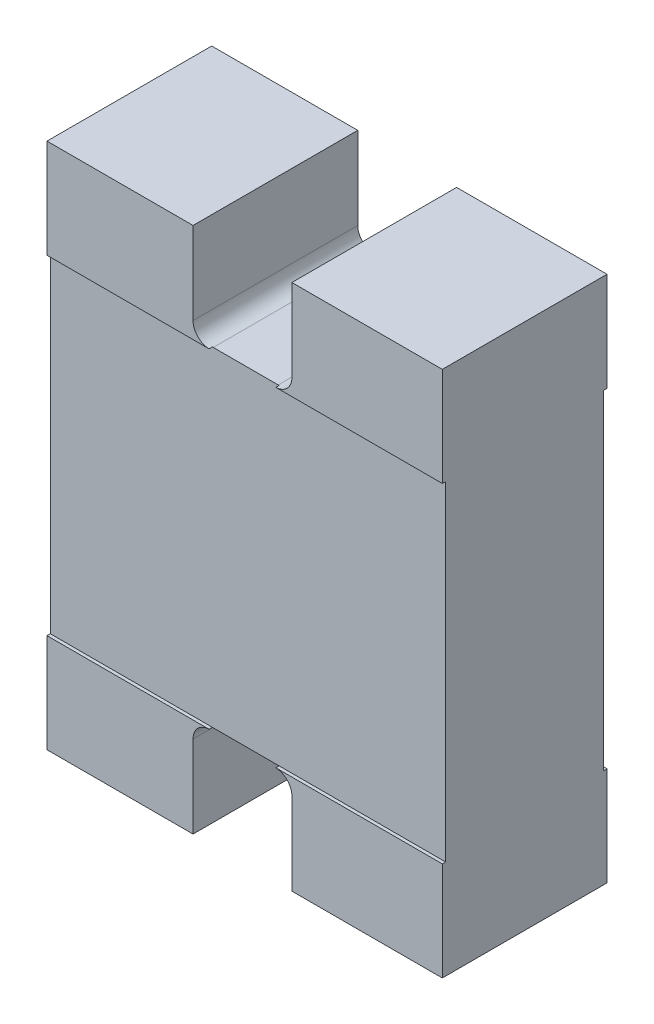
SolidWorks part; units mm, degrees
ref_plane "Front Plane" through (0, 0, 0) normal (0, 0, 1) x (1, 0, 0)
ref_plane "Top Plane" through (0, 0, 0) normal (0, 1, 0) x (1, 0, 0)
ref_plane "Right Plane" through (0, 0, 0) normal (1, 0, 0) x (0, 0, -1)
sketch "Sketch1" plane through (0, 0, 0) normal (0, 0, 1) x (1, 0, 0)
  line L1 (-0.6, 0.8) -> (0.6, 0.8)
  line L2 (-0.6, 0.8) -> (-0.6, -0.8)
  line L3 (-0.6, -0.8) -> (0.6, -0.8)
  line L4 (0.6, 0.8) -> (0.6, -0.8)
  line L5 (-0.6, 0.8) -> (0.6, -0.8) construction
  line L6 (-0.6, -0.8) -> (0.6, 0.8) construction
  point P0 (0, 0)
  dimension "D1" = 1.2
  dimension "D2" = 1.6
extrude "Boss-Extrude1" add sketch "Sketch1" along normal blind 0.5
sketch "Sketch2" plane through (0, 0, 0) normal (0, 0, -1) x (-1, 0, 0)
  line L0 (0, 0.8) -> (0, -0.8) construction
  line L1 (-0.6, 0.8) -> (0.6, 0.8) construction
  line L2 (0.6, -0.8) -> (-0.6, -0.8) construction
  line L3 (-0.6, 0) -> (0.6, 0) construction
  line L4 (-0.6, -0.8) -> (-0.6, 0.8) construction
  line L5 (0.6, 0.8) -> (0.6, -0.8) construction
  line L6 (-0.4, 0.8) -> (-0.4, -0.8) construction
  line L7 (-0.6, 0.5) -> (0.6, 0.5) construction
  line L8 (-0.1434, 0.55) -> (0.1566, 0.55) construction
  line L9 (0.1566, 0.8) -> (0.1566, 0.55)
  line L13 (-0.1434, 0.8) -> (-0.1434, 0.55)
  line L17 (-0.092, 0.5) -> (0.1052, 0.5)
  line L19 (-0.1434, 0.8) -> (0.1566, 0.8)
  arc A0 (0.1566, 0.55) -> (0.1052, 0.5) centre (0.1066, 0.55) cw
  arc A3 (-0.1434, 0.55) -> (-0.092, 0.5) centre (-0.0934, 0.55) ccw
  point P22 (0.1415, 0.5141)
  point P50 (0, 0.5)
  dimension "D4" = 0.05
  dimension "D8" = 0.05
  dimension "D1" = 0.4
  dimension "D2" = 0.3
  dimension "D3" = 0.3
  dimension "D6" = 0.1972
extrude "Cut-Extrude1" cut sketch "Sketch2" against normal through all
sketch "Sketch3" plane through (0, 0, 0) normal (0, 0, -1) x (-1, 0, 0)
  line L0 (-0.6, 0.5) -> (0.6, 0.5) construction
  line L1 (-0.6, -0.8) -> (-0.6, 0.8) construction
  line L2 (0.6, 0.8) -> (0.6, -0.8) construction
  line L3 (-0.6, -0.5) -> (0.6, -0.5) construction
  line L5 (-0.6, 0.5) -> (0.6, 0.5)
  line L6 (-0.6, 0.5) -> (-0.6, -0.5)
  line L7 (-0.6, -0.5) -> (0.6, -0.5)
  line L8 (0.6, 0.5) -> (0.6, -0.5)
extrude "Cut-Extrude2" cut sketch "Sketch3" against normal blind 0.01
ref_plane "Plane1" through (0, 0, 0.25) normal (0, 0, -1) x (-1, 0, 0)
mirror "Mirror0" about plane through (0, 0, 0) normal (0, 1, 0) of "Cut-Extrude1"
mirror "Mirror1" about plane through (0, 0, 0.25) normal (0, 0, -1) of "Cut-Extrude2"
mirror "Mirror3" [suppressed] about plane through (0, 0, 0) normal (1, 0, 0)
sketch "Sketch5" plane through (0, 0, 0.01) normal (0, 0, -1) x (-1, 0, 0)
  line L0 (-0.6, -0.1976) -> (0.6, -0.1976) construction
  line L1 (-0.6, 0.5) -> (-0.6, -0.5) construction
  line L2 (0.6, -0.5) -> (0.6, 0.5) construction
  text T0 "<b>EXB38V  </b>" font "Tahoma" height 0.5
extrude "Boss-Extrude3" [suppressed] add sketch "Sketch5" along normal blind 0.01
